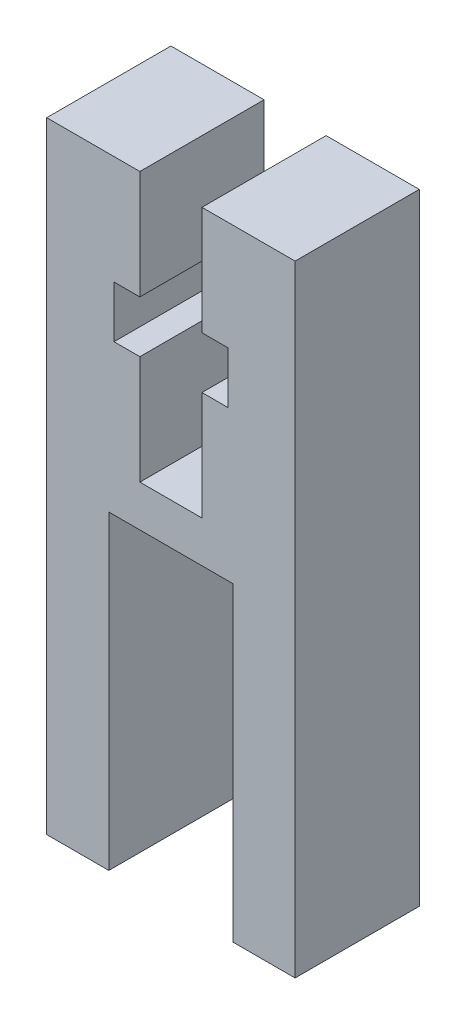
SolidWorks part; units mm, degrees
ref_plane "Спереди" through (0, 0, 0) normal (0, 0, 1) x (1, 0, 0)
ref_plane "Сверху" through (0, 0, 0) normal (0, 1, 0) x (1, 0, 0)
ref_plane "Справа" through (0, 0, 0) normal (1, 0, 0) x (0, 0, -1)
other "Configuration Table"
sketch "Эскиз1" plane through (0, 0, 0) normal (0, 0, 1) x (1, 0, 0)
  line L0 (0, 0) -> (0, 30) construction
  line L1 (0, 15) -> (-21.3565, 15) construction
  line L2 (-1.5, 30) -> (-1.5, 24.75)
  line L3 (-1.5, 24.75) -> (-2.75, 24.75)
  line L4 (-2.75, 24.75) -> (-2.75, 22.25)
  line L5 (-2.75, 22.25) -> (-1.5, 22.25)
  line L6 (-1.5, 22.25) -> (-1.5, 17)
  line L7 (-1.5, 17) -> (1.5, 17)
  line L8 (1.5, 22.25) -> (1.5, 17)
  line L9 (2.75, 22.25) -> (1.5, 22.25)
  line L10 (2.75, 24.75) -> (2.75, 22.25)
  line L11 (1.5, 24.75) -> (2.75, 24.75)
  line L12 (1.5, 30) -> (1.5, 24.75)
  line L25 (-1.5, 30) -> (-6, 30)
  line L26 (-6, 30) -> (-6, 0)
  line L28 (6, 30) -> (6, 0)
  line L29 (1.5, 30) -> (6, 30)
  line L30 (-6, 0) -> (-3, 0)
  line L31 (-3, 0) -> (-3, 15)
  line L32 (-3, 15) -> (3, 15)
  line L33 (3, 0) -> (3, 15)
  line L34 (6, 0) -> (3, 0)
  point P13 (0, 17)
  point P18 (2.75, 23.5)
  point P23 (0, 15)
  dimension "D1" = 2.5
  dimension "D2" = 3
  dimension "D3" = 5.5
  dimension "D4" = 13
  dimension "D5" = 6
  dimension "D6" = 12
  dimension "D7" = 30
extrude "Бобышка-Вытянуть1" add sketch "Эскиз1" along normal blind 6
